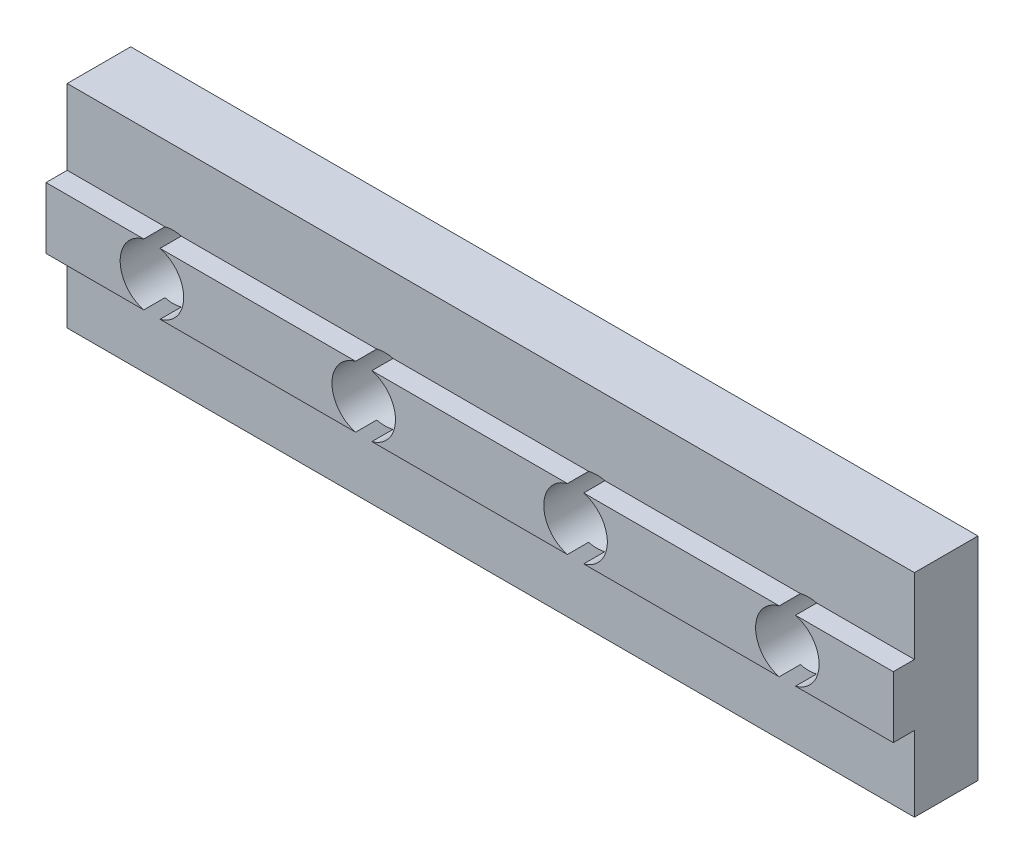
SolidWorks part; units mm, degrees
ref_plane "Front Plane" through (0, 0, 0) normal (0, 0, 1) x (1, 0, 0)
ref_plane "Top Plane" through (0, 0, 0) normal (0, 1, 0) x (1, 0, 0)
ref_plane "Right Plane" through (0, 0, 0) normal (1, 0, 0) x (0, 0, -1)
sketch "Esquisse1" plane through (0, 0, 0) normal (0, 0, 1) x (1, 0, 0)
  line L1 (0, 0) -> (40, 0)
  line L2 (0, 0) -> (0, 10)
  line L3 (0, 10) -> (40, 10)
  line L4 (40, 0) -> (40, 10)
  point P15 (0, 5)
  point P17 (40, 5)
  dimension "D1" = 40
  dimension "D2" = 10
extrude "Boss.-Extru.1" add sketch "Esquisse1" along normal blind 3
sketch "Esquisse2" plane through (0, 0, 3) normal (0, 0, 1) x (1, 0, 0)
  line L0 (40, 0) -> (40, 10) construction
  line L1 (40, 3.55) -> (0, 3.55)
  line L2 (40, 3.55) -> (40, 6.45)
  line L3 (40, 6.45) -> (0, 6.45)
  line L4 (0, 3.55) -> (0, 6.45)
  line L5 (0, 10) -> (0, 0) construction
  line L6 (0, 10) -> (0, 0) construction
  point P8 (0, 5)
  point P9 (0, 5)
  point P12 (0, 0)
  point P15 (0, 5)
  dimension "D1" = 2.9
extrude "Boss.-Extru.2" add sketch "Esquisse2" along normal blind 1
sketch "Esquisse3" plane through (0, 0, 0) normal (0, 0, -1) x (-1, 0, 0)
  line L0 (-40, 0) -> (-40, 10) construction
  circle A0 centre (-35, 5) radius 1.5
  point P2 (0, 0)
  point P5 (-40, 5)
  dimension "D1" = 3
  dimension "D2" = 5
extrude "Enlèv. mat.-Extru.1" cut sketch "Esquisse3" against normal through all
pattern_linear "Répétition linéaire1" count 4 spacing 10 along (-1, 0, 0) of "Enlèv. mat.-Extru.1"
